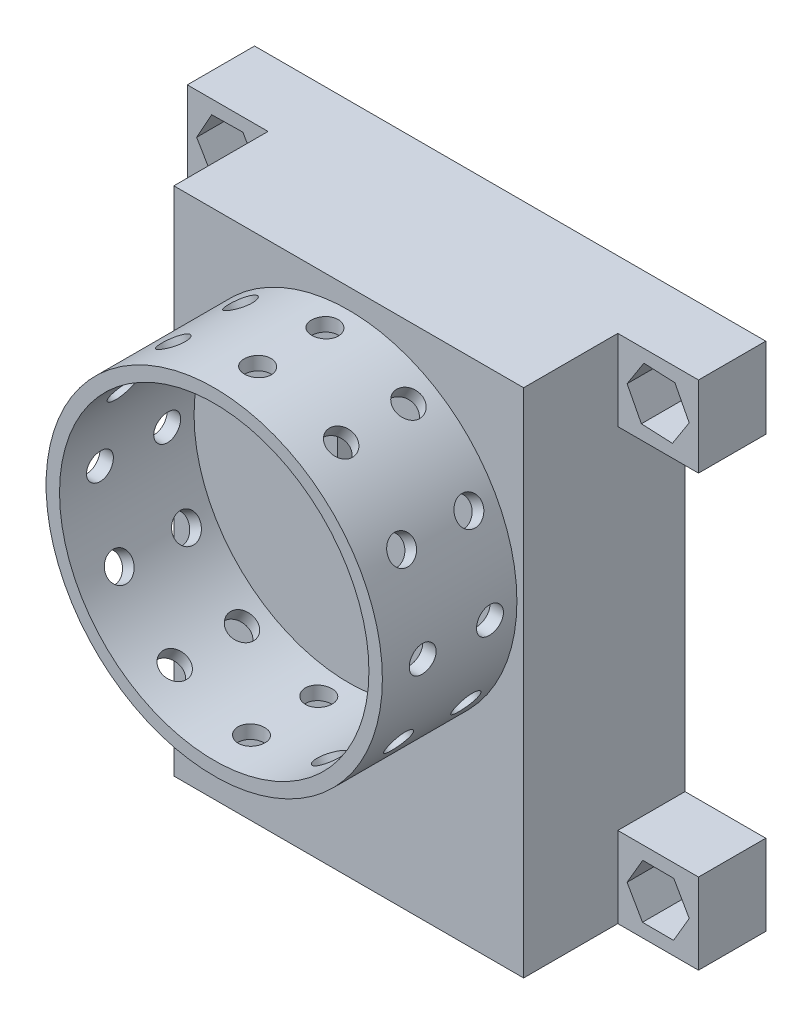
SolidWorks part; units mm, degrees
ref_plane "正面" through (0, 0, 0) normal (0, 0, 1) x (1, 0, 0)
ref_plane "平面" through (0, 0, 0) normal (0, 1, 0) x (1, 0, 0)
ref_plane "右側面" through (0, 0, 0) normal (1, 0, 0) x (0, 0, -1)
sketch "ｽｹｯﾁ1" plane through (0, 0, 0) normal (0, 0, 1) x (1, 0, 0)
  line L1 (13, -19) -> (-13, -19)
  line L2 (13, -19) -> (13, 19)
  line L3 (13, 19) -> (-13, 19)
  line L4 (-13, -19) -> (-13, 19)
  line L5 (13, -19) -> (-13, 19) construction
  line L6 (13, 19) -> (-13, -19) construction
  point P0 (0, 0)
  dimension "D1" = 38
  dimension "D2" = 26
extrude "ﾎﾞｽ - 押し出し1" add sketch "ｽｹｯﾁ1" along normal blind 12
sketch "ｽｹｯﾁ2" plane through (0, 0, 0) normal (0, 0, 1) x (1, 0, 0)
  line L1 (11, -17) -> (-11, -17)
  line L2 (11, -17) -> (11, 17)
  line L3 (11, 17) -> (-11, 17)
  line L4 (-11, -17) -> (-11, 17)
  line L5 (11, -17) -> (-11, 17) construction
  line L6 (11, 17) -> (-11, -17) construction
  point P0 (0, 0)
  dimension "D1" = 22
  dimension "D2" = 34
extrude "ｶｯﾄ - 押し出し1" cut sketch "ｽｹｯﾁ2" along normal blind 10
sketch "ｽｹｯﾁ3" plane through (0, 0, 0) normal (0, 0, 1) x (1, 0, 0)
  line L0 (13, 19) -> (-13, 19) construction
  line L1 (-0.8522, 2) -> (1.1478, 2)
  line L2 (-0.8522, 2) -> (-0.8522, 9)
  line L3 (-0.8522, 9) -> (1.1478, 9)
  line L4 (1.1478, 2) -> (1.1478, 9)
  line L5 (-0.8522, 2) -> (1.1478, 9) construction
  line L6 (-0.8522, 9) -> (1.1478, 2) construction
  point P0 (0.1478, 5.5)
  dimension "D1" = 7
  dimension "D2" = 2
  dimension "D3" = 10
extrude "ｶｯﾄ - 押し出し3" cut sketch "ｽｹｯﾁ3" along normal blind 12
sketch "ｽｹｯﾁ4" plane through (0, 0, 0) normal (0, 0, 1) x (1, 0, 0)
  line L0 (13, -19) -> (13, 19) construction
  line L1 (13, 19) -> (19, 19)
  line L2 (13, 19) -> (13, 13)
  line L3 (13, 13) -> (19, 13)
  line L4 (19, 19) -> (19, 13)
  line L5 (13, -19) -> (19, -19)
  line L6 (13, -19) -> (13, -13)
  line L7 (13, -13) -> (19, -13)
  line L8 (19, -19) -> (19, -13)
  line L9 (-13, -19) -> (13, -19) construction
  line L10 (-13, -19) -> (-19, -19)
  line L11 (-13, -19) -> (-13, -13)
  line L12 (-13, -13) -> (-19, -13)
  line L13 (-19, -19) -> (-19, -13)
  line L14 (-13, 19) -> (-19, 19)
  line L15 (-13, 19) -> (-13, 13)
  line L16 (-13, 13) -> (-19, 13)
  line L17 (-19, 19) -> (-19, 13)
  dimension "D1" = 6
  dimension "D2" = 6
  dimension "D3" = 6
  dimension "D4" = 6
  dimension "D5" = 6
  dimension "D6" = 6
  dimension "D7" = 6
  dimension "D8" = 6
  dimension "D9" = 6
extrude "ﾎﾞｽ - 押し出し2" add sketch "ｽｹｯﾁ4" along normal blind 5
sketch "ｽｹｯﾁ5" plane through (0, 0, 0) normal (0, 0, 1) x (1, 0, 0)
  line L0 (-13, 19) -> (-19, 19) construction
  line L1 (-19, 19) -> (-19, 13) construction
  line L2 (-13, -13) -> (-19, -13) construction
  line L3 (19, -19) -> (19, -13) construction
  line L5 (13, 13) -> (19, 13) construction
  line L7 (19, -13) -> (13, -13) construction
  circle A0 centre (-16, 16) radius 1
  circle A1 centre (-16, -16) radius 1
  circle A2 centre (16, -16) radius 1
  circle A3 centre (16, 16) radius 1
  point P16 (16, 13)
  dimension "D1" = 3
  dimension "D2" = 3
  dimension "D3" = 3
  dimension "D4" = 2
  dimension "D5" = 2
  dimension "D6" = 3
  dimension "D7" = 2
  dimension "D8" = 2
  dimension "D9" = 3
  dimension "D10" = 3
extrude "ｶｯﾄ - 押し出し4" cut sketch "ｽｹｯﾁ5" along normal through all
sketch "ｽｹｯﾁ6" plane through (0, 0, 0) normal (0, 0, 1) x (1, 0, 0)
  line L0 (-19, 19) -> (-19, 13) construction
  line L1 (-17.1841, 17.9827) -> (-18.3091, 15.9659)
  line L2 (-18.3091, 15.9659) -> (-17.125, 13.9832)
  line L3 (-17.125, 13.9832) -> (-14.8159, 14.0173)
  line L4 (-14.8159, 14.0173) -> (-13.6909, 16.0341)
  line L5 (-13.6909, 16.0341) -> (-14.875, 18.0168)
  line L6 (-14.875, 18.0168) -> (-17.1841, 17.9827)
  line L7 (-19, -19) -> (-13, -19) construction
  line L8 (-17.0756, -13.9564) -> (-18.3076, -15.9097)
  line L9 (-18.3076, -15.9097) -> (-17.232, -17.9533)
  line L10 (-17.232, -17.9533) -> (-14.9244, -18.0436)
  line L11 (-14.9244, -18.0436) -> (-13.6924, -16.0903)
  line L12 (-13.6924, -16.0903) -> (-14.768, -14.0467)
  line L13 (-14.768, -14.0467) -> (-17.0756, -13.9564)
  line L14 (-13, 19) -> (-19, 19) construction
  line L15 (19, 19) -> (13, 19) construction
  line L16 (14.9393, 18.0514) -> (13.6931, 16.1072)
  line L17 (13.6931, 16.1072) -> (14.7537, 14.0557)
  line L18 (14.7537, 14.0557) -> (17.0607, 13.9486)
  line L19 (17.0607, 13.9486) -> (18.3069, 15.8928)
  line L20 (18.3069, 15.8928) -> (17.2463, 17.9443)
  line L21 (17.2463, 17.9443) -> (14.9393, 18.0514)
  line L22 (19, 13) -> (19, 19) construction
  line L23 (19, -19) -> (19, -13) construction
  line L24 (14.8545, -13.9947) -> (13.6906, -15.9894)
  line L25 (13.6906, -15.9894) -> (14.8362, -17.9947)
  line L26 (14.8362, -17.9947) -> (17.1455, -18.0053)
  line L27 (17.1455, -18.0053) -> (18.3094, -16.0106)
  line L28 (18.3094, -16.0106) -> (17.1638, -14.0053)
  line L29 (17.1638, -14.0053) -> (14.8545, -13.9947)
  line L30 (19, -13) -> (13, -13) construction
  line L31 (-19, -13) -> (-19, -19) construction
  circle A0 centre (-16, 16) radius 2 construction
  circle A1 centre (-16, -16) radius 2 construction
  circle A2 centre (16, 16) radius 2 construction
  circle A3 centre (16, -16) radius 2 construction
  point P23 (16, 19)
  point P45 (16, -13)
  dimension "D1" = 4
  dimension "D3" = 4
  dimension "D6" = 4
  dimension "D9" = 4
  dimension "D2" = 3
  dimension "D4" = 3
  dimension "D5" = 3
  dimension "D7" = 3
  dimension "D8" = 3
  dimension "D10" = 3
  dimension "D11" = 3
  dimension "D12" = 3
extrude "ｶｯﾄ - 押し出し5" cut sketch "ｽｹｯﾁ6" along normal blind 4 from offset 1
sketch "ｽｹｯﾁ7" plane through (0, 0, 12) normal (0, 0, 1) x (1, 0, 0)
  line L0 (-13, 19) -> (-13, -19) construction
  line L1 (13, 19) -> (-13, 19) construction
  circle A0 centre (0, 5) radius 12.5
  circle A1 centre (0, 5) radius 11.5
  dimension "D1" = 25
  dimension "D4" = 23
  dimension "D2" = 13
  dimension "D3" = 14
extrude "ﾎﾞｽ - 押し出し3" add sketch "ｽｹｯﾁ7" along normal blind 10
sketch "ｽｹｯﾁ8" plane through (0, 0, 0) normal (1, 0, 0) x (0, 0, -1)
  line L0 (-22, 17.5) -> (-22, -7.5) construction
  circle A0 centre (-19, 5.2266) radius 1
  dimension "D1" = 2
  dimension "D2" = 3
extrude "ｶｯﾄ - 押し出し6" cut sketch "ｽｹｯﾁ8" against normal blind 20
pattern_linear "直線ﾊﾟﾀｰﾝ1" count 2 spacing 5 along (0, 0, -1) of "ｶｯﾄ - 押し出し6"
pattern_circular "円形ﾊﾟﾀｰﾝ1" count 12 over 360 about axis through (0, 5, 22) along (0, 0, -1) of "直線ﾊﾟﾀｰﾝ1", "ｶｯﾄ - 押し出し6"
